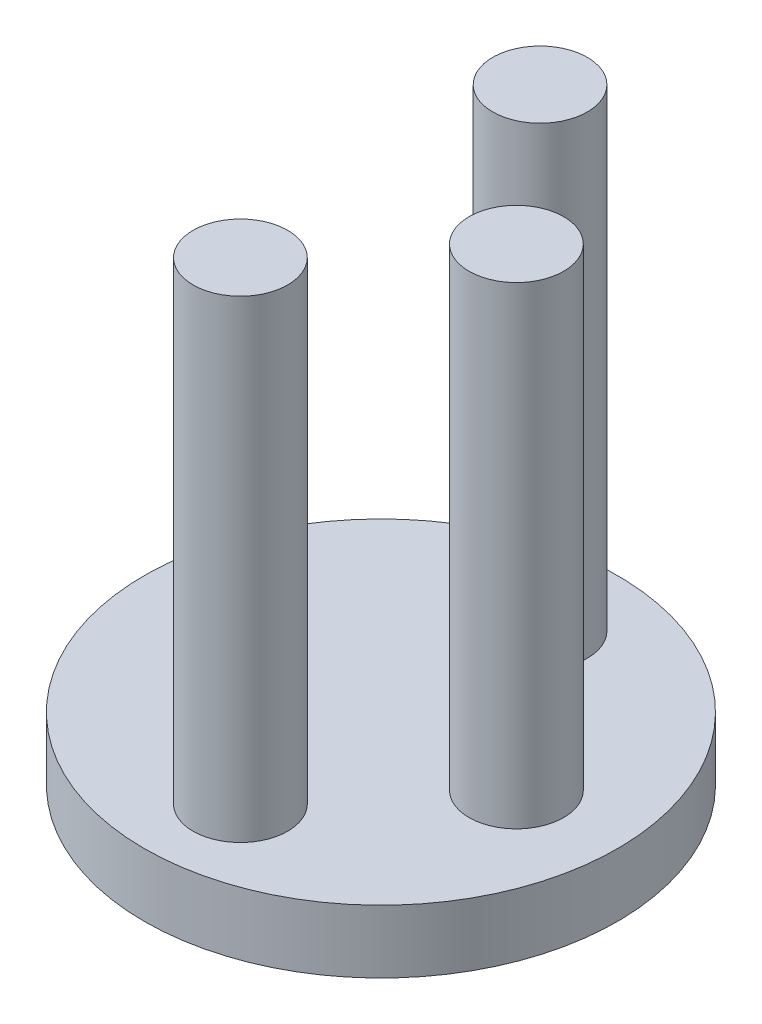
SolidWorks part; units mm, degrees
ref_plane "Front Plane" through (0, 0, 0) normal (0, 0, 1) x (1, 0, 0)
ref_plane "Top Plane" through (0, 0, 0) normal (0, 1, 0) x (1, 0, 0)
ref_plane "Right Plane" through (0, 0, 0) normal (1, 0, 0) x (0, 0, -1)
sketch "Sketch1" plane through (0, 0, 0) normal (0, 1, 0) x (1, 0, 0)
  circle A0 centre (0, 0) radius 7.5
  dimension "D1" = 15
extrude "Boss-Extrude1" add sketch "Sketch1" along normal blind 2
sketch "Sketch2" plane through (0, 2, 0) normal (0, 1, 0) x (1, 0, 0)
  line L0 (4.2941, 0) -> (-3.7059, 0) construction
  line L1 (0.2941, 4.75) -> (0.2941, -4.75) construction
  circle A0 centre (0.2941, -4.75) radius 1.5
  circle A1 centre (0.2941, 4.75) radius 1.5
  circle A2 centre (4.2941, 0) radius 1.5
  point P6 (0.2941, 0)
  point P9 (0.2941, 0)
  dimension "D1" = 3
  dimension "D2" = 9.5
  dimension "D3" = 4
extrude "Boss-Extrude2" add sketch "Sketch2" along normal blind 15
